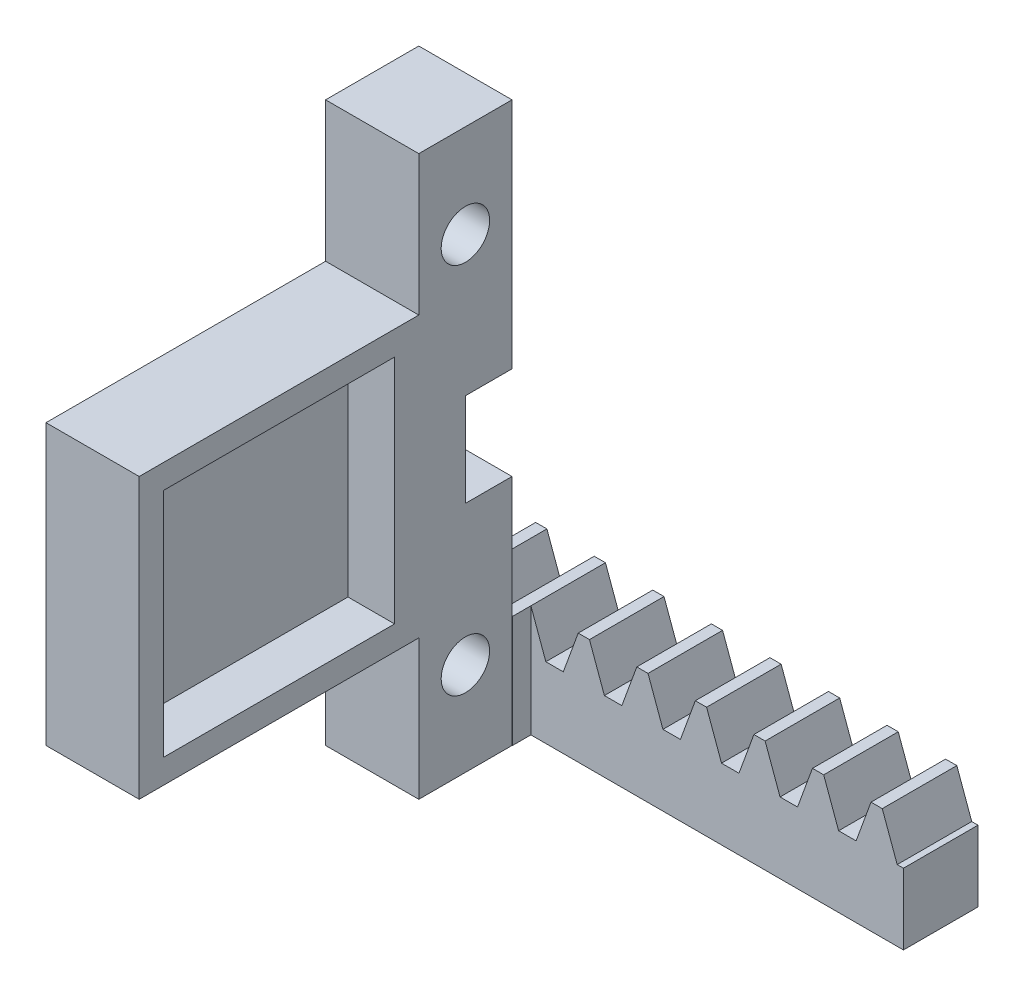
SolidWorks part; units mm, degrees
extrude "Blank" add sketch "BlankSke" against normal blind 6.35
sketch "BlankSke" plane through (0, 0, 0) normal (0, 0, 1) x (1, 0, 0)
  line L1 (0, 0) -> (31.75, 0)
  line L2 (0, 0) -> (0, 7.62)
  line L3 (0, 7.62) -> (31.75, 7.62)
  line L4 (31.75, 0) -> (31.75, 7.62)
  dimension "Length" = 31.75
  dimension "Blank_height" = 7.62
ref_plane "Plane1" through (0, 0, 0) normal (0, 0, 1) x (1, 0, 0)
ref_plane "Plane2" through (0, 0, 0) normal (0, 1, 0) x (1, 0, 0)
ref_plane "Plane3" through (0, 0, 0) normal (1, 0, 0) x (0, 0, -1)
other "Configuration Table"
sketch "HoldingSke" plane through (0, 0, 0) normal (0, 1, 0) x (1, 0, 0)
  line L0 (0, 0) -> (389.1506, -326.5361)
  line L1 (-15, 0) -> (100, 0) construction
  line L2 (0, 0) -> (-2.1039, 2.3779)
  line L3 (0, 0) -> (-11.863, 4.5341)
  line L4 (0, 0) -> (8.5297, 1.351)
  line L5 (0, 0) -> (-23.7986, -8.8762)
  line L6 (0, 0) -> (-10.5278, -7.1032)
  line L9 (-71.009, 38.7566) -> (-41.1737, 49.6157)
  line L10 (-76.2, 71.12) -> (-69.85, 71.12)
  line L11 (0, 0) -> (-6.35, 0)
  line L12 (-76.2, 101.6) -> (-76.1492, 101.6)
  line L13 (24.9733, 27.94) -> (52.9518, 28.4284)
  line L14 (24.9733, 27.94) -> (25.0241, 27.9398)
  line L15 (24.9733, 27.94) -> (100.4021, 29.52)
  circle A0 centre (0, 0) radius 19.05
  circle A1 centre (0, 0) radius 3.175
  circle A2 centre (0, 0) radius 12.7
  dimension "MPH" = 6.35
  dimension "Diameter" = 38.1
  dimension "Num_teeth" = 9
  dimension "Pitch" = 508
  dimension "Show_teeth" = 400
  dimension "Thickness" = 12.7
  dimension "Ap" = 20
  dimension "Pitch_height" = 6.35
  dimension "Width" = 6.35
  dimension "Backlash" = 0.0508
  dimension "Addendum_fac" = 1
  dimension "Dedendum_fac" = 1.2
  dimension "Clearance_fac" = 0.2
  dimension "Dedendum_add" = 0.0508
  dimension "Length" = 31.75
sketch "TooCutSkeIll" plane through (0, 0, 0) normal (0, 0, 1) x (1, 0, 0)
  line L0 (-1.5999, 7.5866) -> (-0.6682, 5.0266)
  line L1 (-0.3817, 4.826) -> (0.3817, 4.826)
  line L2 (0.6682, 5.0266) -> (1.5999, 7.5866)
  line L3 (31.75, 7.62) -> (0, 7.62) construction
  line L4 (0, 0) -> (0, 64.897) construction
  line L5 (-13.208, 6.35) -> (12.954, 6.35) construction
  line L6 (0, 0) -> (31.75, 0) construction
  line L7 (1.1499, 6.35) -> (1.1499, 48.7463) construction
  line L8 (-1.1499, 6.35) -> (-1.1499, 48.7463) construction
  line L9 (1.6477, 7.62) -> (1.6477, 7.6454)
  line L10 (-1.6477, 7.62) -> (-1.6477, 7.6454)
  line L11 (-1.6477, 7.6454) -> (1.6477, 7.6454)
  arc A0 (0.3817, 4.826) -> (0.6682, 5.0266) centre (0.3817, 5.1308) ccw
  arc A1 (-0.6682, 5.0266) -> (-0.3817, 4.826) centre (-0.3817, 5.1308) ccw
  arc A2 (1.6477, 7.62) -> (1.5999, 7.5866) centre (1.6477, 7.5692) ccw
  arc A3 (-1.5999, 7.5866) -> (-1.6477, 7.62) centre (-1.6477, 7.5692) ccw
  dimension "Pitch_height" = 6.35
  dimension "Addendum_plus" = 1.2954
  dimension "Pressure_angle" = 20
  dimension "Gap_width" = 2.2997
  dimension "Dedendum" = 1.524
extrude "ToothCutIll" [suppressed] cut sketch "TooCutSkeIll" against normal through all
sketch "TooCutSkeSim" plane through (0, 0, 0) normal (0, 0, 1) x (1, 0, 0)
  line L0 (0.5952, 4.826) -> (-0.5952, 4.826)
  line L1 (1.6213, 7.6454) -> (0.5952, 4.826)
  line L2 (0, 17.4625) -> (0, 53.467) construction
  line L3 (1.6213, 7.6454) -> (-1.6213, 7.6454)
  line L6 (-1.6213, 7.6454) -> (-0.5952, 4.826)
  line L9 (-1.1499, 6.35) -> (1.1499, 6.35) construction
  line L10 (0, 0) -> (31.75, 0) construction
  line L11 (1.1499, 6.35) -> (1.1499, 53.467) construction
  line L12 (-1.1499, 6.35) -> (-1.1499, 53.467) construction
  dimension "Pitch_height" = 6.35
  dimension "Addendum_plus" = 1.2954
  dimension "Pressure_angle" = 20
  dimension "Gap_width" = 2.2997
  dimension "Dedendum" = 1.524
extrude "ToothCutSim" cut sketch "TooCutSkeSim" against normal through all
pattern_linear "TeethCuts" count 9 spacing 3.9898 along (1, 0, 0) of "ToothCutIll", "ToothCutSim"
sketch "Sketch1" plane through (0, 0, 0) normal (0, 0, 1) x (1, 0, 0)
  line L1 (0, 0) -> (6.35, 0)
  line L2 (0, 0) -> (0, 12.7)
  line L3 (0, 12.7) -> (6.35, 12.7)
  line L4 (6.35, 0) -> (6.35, 12.7)
  dimension "D1" = 6.35
  dimension "D2" = 12.7
extrude "Boss-Extrude1" add sketch "Sketch1" along normal blind 6.35
sketch "Sketch2" plane through (0, 0, 0) normal (-1, 0, 0) x (0, 0, 1)
  line L0 (3.175, 12.7) -> (3.175, 0) construction
  line L1 (6.35, 12.7) -> (0, 12.7) construction
  line L2 (-6.35, 0) -> (6.35, 0) construction
  circle A0 centre (3.175, 6.35) radius 1.65
  dimension "D1" = 3.3
  dimension "D2" = 6.35
extrude "Cut-Extrude1" cut sketch "Sketch2" against normal up to surface (6.35 mm away) up to face at (6.35, 6.604, 2.54)
sketch "Sketch3" plane through (0, 0, 6.35) normal (0, 0, 1) x (1, 0, 0)
  line L0 (6.35, 0) -> (6.35, 12.7) construction
  line L1 (6.35, 9.525) -> (0, 9.525)
  line L2 (6.35, 9.525) -> (6.35, 12.7)
  line L3 (6.35, 12.7) -> (0, 12.7)
  line L4 (0, 9.525) -> (0, 12.7)
  line L6 (0, 12.7) -> (0, 0) construction
  line L7 (6.35, 12.7) -> (0, 12.7) construction
  dimension "D2" = 3.175
sketch "Sketch4" plane through (0, 0, 6.35) normal (0, 0, 1) x (1, 0, 0)
  line L1 (0, 9.525) -> (6.35, 9.525)
  line L2 (0, 9.525) -> (0, 28.575)
  line L3 (0, 28.575) -> (6.35, 28.575)
  line L4 (6.35, 9.525) -> (6.35, 28.575)
  line L5 (6.35, 0) -> (6.35, 12.7) construction
  dimension "D1" = 19.05
extrude "Boss-Extrude3" add sketch "Sketch4" along normal blind 19.05
sketch "Sketch5" plane through (0, 0, 6.35) normal (0, 0, -1) x (-1, 0, 0)
  line L0 (0, 28.575) -> (0, 12.7) construction
  line L1 (-6.35, 28.575) -> (0, 28.575)
  line L2 (-6.35, 28.575) -> (-6.35, 25.4)
  line L3 (-6.35, 25.4) -> (0, 25.4)
  line L4 (0, 28.575) -> (0, 25.4)
  dimension "D1" = 3.175
sketch "Sketch6" plane through (6.35, 0, 0) normal (1, 0, 0) x (0, 0, -1)
  line L0 (-6.35, 12.7) -> (-6.35, 28.575) construction
  line L1 (-6.35, 25.4) -> (0, 25.4)
  line L2 (-6.35, 25.4) -> (-6.35, 38.1)
  line L3 (-6.35, 38.1) -> (0, 38.1)
  line L4 (0, 25.4) -> (0, 38.1)
  line L5 (-25.4, 28.575) -> (-6.35, 28.575) construction
  dimension "D1" = 12.7
  dimension "D2" = 6.35
  dimension "D3" = 3.175
extrude "Boss-Extrude5" add sketch "Sketch6" against normal up to surface (6.35 mm away) up to face at (0, 6.35, 4.825)
sketch "Sketch7" plane through (6.35, 0, 0) normal (1, 0, 0) x (0, 0, -1)
  line L0 (-3.175, 38.1) -> (-3.175, 25.4) construction
  line L1 (0, 38.1) -> (-6.35, 38.1) construction
  line L3 (-6.35, 25.4) -> (0, 25.4) construction
  circle A0 centre (-3.175, 31.75) radius 1.65
  dimension "D1" = 3.3
extrude "Cut-Extrude2" cut sketch "Sketch7" against normal up to surface (6.35 mm away) up to face at (0, 6.35, 4.825)
sketch "Sketch8" plane through (6.35, 0, 0) normal (1, 0, 0) x (0, 0, -1)
  line L0 (-25.4, 19.05) -> (-6.35, 19.05) construction
  line L1 (-25.4, 9.525) -> (-25.4, 28.575) construction
  line L2 (-6.35, 12.7) -> (-6.35, 25.4) construction
  line L4 (-23.749, 26.924) -> (-8.001, 26.924)
  line L5 (-23.749, 26.924) -> (-23.749, 11.176)
  line L6 (-23.749, 11.176) -> (-8.001, 11.176)
  line L7 (-8.001, 26.924) -> (-8.001, 11.176)
  point P10 (-8.001, 19.05)
  point P11 (-15.875, 26.924)
  point P12 (-15.875, 19.05)
  dimension "D1" = 15.748
extrude "Cut-Extrude3" cut sketch "Sketch8" against normal blind 3.175
sketch "Sketch9" plane through (0, 12.7, 0) normal (0, 1, 0) x (1, 0, 0)
  line L1 (0, 0) -> (6.35, 0)
  line L2 (0, 0) -> (0, -6.35)
  line L3 (0, -6.35) -> (6.35, -6.35)
  line L4 (6.35, 0) -> (6.35, -6.35)
sketch "Sketch11" plane through (0, 12.7, 0) normal (0, 1, 0) x (1, 0, 0)
  line L1 (0, 0) -> (6.35, 0)
  line L2 (0, 0) -> (0, -6.35)
  line L3 (0, -6.35) -> (6.35, -6.35)
  line L4 (6.35, 0) -> (6.35, -6.35)
extrude "Boss-Extrude7" add sketch "Sketch11" along normal up to surface (12.7 mm away) up to face at (3.175, 25.4, 3.175)
sketch "Sketch12" plane through (6.35, 0, 0) normal (1, 0, 0) x (0, 0, -1)
  line L1 (-3.175, 15.875) -> (0, 15.875)
  line L2 (-3.175, 15.875) -> (-3.175, 22.225)
  line L3 (-3.175, 22.225) -> (0, 22.225)
  line L4 (0, 15.875) -> (0, 22.225)
  line L5 (0, 7.62) -> (0, 38.1) construction
  line L6 (-25.4, 19.05) -> (0, 19.05) construction
  line L7 (-25.4, 9.525) -> (-25.4, 28.575) construction
  point P4 (0, 19.05)
  dimension "D1" = 6.35
  dimension "D2" = 3.175
extrude "Cut-Extrude4" cut sketch "Sketch12" against normal up to surface (6.35 mm away) up to face at (0, 16.2052, 6.35)
sketch "Sketch13" plane through (0, 0, 0) normal (0, 0, 1) x (1, 0, 0)
  line L1 (6.3675, 7.62) -> (31.75, 7.62)
  line L2 (6.3675, 7.62) -> (6.3675, 0)
  line L3 (6.3675, 0) -> (31.75, 0)
  line L4 (31.75, 7.62) -> (31.75, 0)
extrude "Cut-Extrude5" cut sketch "Sketch13" against normal blind 1.27
equation "' \"Pitch@HoldingSke\" = 4"
equation "' \"Num_teeth@HoldingSke\" = 12"
equation "' \"Ap@HoldingSke\" =  20"
equation "' \"Ap@HoldingSke\" = 20"
equation "' \"Width@HoldingSke\" = 0.25"
equation "' \"Show_teeth@HoldingSke\" = 500"
equation "' \"Backlash@HoldingSke\" = 0.009"
equation "' \"Addendum_fac@HoldingSke\" = 1.0"
equation "' \"Dedendum_fac@HoldingSke\" = 1.25"
equation "' \"Dedendum_add@HoldingSke\" = 0.00005"
equation "' \"Clearance_fac@HoldingSke\" = 0.25"
equation "' \"Pitch_height@HoldingSke\" = 1"
equation "' \"Length@HoldingSke\" = 4.71"
equation "\"MPH@HoldingSke\" = \"Dedendum_fac@HoldingSke\" / \"Pitch@HoldingSke\" + 2 * \"Dedendum_add@HoldingSke\" + 0.002"
equation "\"MPH@HoldingSke\" = ((sgn( \"MPH@HoldingSke\" - \"Pitch_height@HoldingSke\")+1)*( \"MPH@HoldingSke\" - \"Pitch_height@HoldingSke\"))/2 + \"Pitch_height@HoldingSke\""
equation "\"Blank_height@BlankSke\" = \"Pitch_height@HoldingSke\" + \"Addendum_fac@HoldingSke\"  / \"Pitch@HoldingSke\" "
equation "\"Length@BlankSke\" =  \"Length@HoldingSke\""
equation "\"Face_width@Blank\" = \"Width@HoldingSke\""
equation "\"Pressure_angle@TooCutSkeIll\" = \"Ap@HoldingSke\""
equation "\"Addendum_plus@TooCutSkeIll\" =  \"Addendum_fac@HoldingSke\"  / \"Pitch@HoldingSke\" + 0.001"
equation "\"Dedendum@TooCutSkeIll\" = \"Dedendum_fac@HoldingSke\"  / \"Pitch@HoldingSke\""
equation "\"Pitch_height@TooCutSkeIll\" =  \"MPH@HoldingSke\""
equation "\"Gap_width@TooCutSkeIll\" = 3.14159265 / 2 / \"Pitch@HoldingSke\" + 6 * \"Backlash@HoldingSke\""
equation "\"Pressure_angle@TooCutSkeSim\" = \"Ap@HoldingSke\""
equation "\"Addendum_plus@TooCutSkeSim\" =  \"Addendum_fac@HoldingSke\"  / \"Pitch@HoldingSke\" + 0.001"
equation "\"Dedendum@TooCutSkeSim\" = \"Dedendum_fac@HoldingSke\"  / \"Pitch@HoldingSke\""
equation "\"Pitch_height@TooCutSkeSim\" =  \"MPH@HoldingSke\""
equation "\"Gap_width@TooCutSkeSim\" = 3.14159265 / 2 / \"Pitch@HoldingSke\" + 6 * \"Backlash@HoldingSke\""
equation "\"Root_fillet@TooCutSkeIll\" = \"Clearance_fac@HoldingSke\" / \"Pitch@HoldingSke\" + \"Dedendum_add@HoldingSke\""
equation "\"Break_rad@TooCutSkeIll\" = 0.02 / \"Pitch@HoldingSke\" * 2"
equation "\"Linear_pitch@TeethCuts\" = 3.14159265 / \"Pitch@HoldingSke\""
equation "\"Num_teeth@HoldingSke\" = int( ( \"Length@HoldingSke\" + 0 ) / (3.14159265 / \"Pitch@HoldingSke\")) + 0.9999  + 1"
equation " \"Num_teeth@TeethCuts\" = int( \"Show_teeth@HoldingSke\" ) + 1"
equation " \"Num_teeth@TeethCuts\" = ((sgn( \"Num_teeth@TeethCuts\" - \"Num_teeth@HoldingSke\" )-1)*( \"Num_teeth@TeethCuts\" - \"Num_teeth@HoldingSke\" ))/-2+ \"Num_teeth@HoldingSke\""
equation " \"Num_teeth@TeethCuts\" = ((sgn( \"Num_teeth@TeethCuts\" - 2.0)+1)*( \"Num_teeth@TeethCuts\" - 2.0))/2 +2.0"
